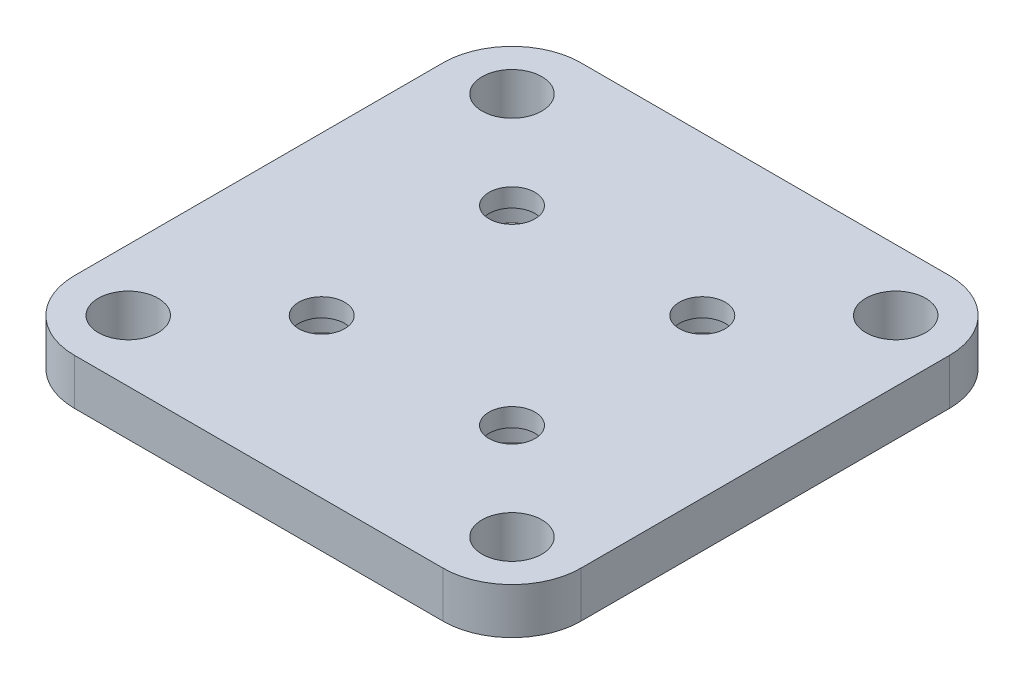
SolidWorks part; units mm, degrees
ref_plane "Front Plane" through (0, 0, 0) normal (0, 0, 1) x (1, 0, 0)
ref_plane "Top Plane" through (0, 0, 0) normal (0, 1, 0) x (1, 0, 0)
ref_plane "Right Plane" through (0, 0, 0) normal (1, 0, 0) x (0, 0, -1)
sketch "Sketch1" plane through (0, 0, 0) normal (0, 1, 0) x (1, 0, 0)
  line L1 (-27.55, -27.55) -> (27.55, -27.55)
  line L2 (-27.55, -27.55) -> (-27.55, 27.55)
  line L3 (-27.55, 27.55) -> (27.55, 27.55)
  line L4 (27.55, -27.55) -> (27.55, 27.55)
  line L5 (-27.55, -27.55) -> (27.55, 27.55) construction
  line L6 (-27.55, 27.55) -> (27.55, -27.55) construction
  point P0 (0, 0)
  dimension "D1" = 55.1
  dimension "D2" = 55.1
extrude "Boss-Extrude1" add sketch "Sketch1" along normal blind 5
fillet "Fillet1" radius 7.5 4 edges at (-27.55, 2.5, 27.55) (-27.55, 2.5, -27.55) (27.55, 2.5, -27.55) (27.55, 2.5, 27.55)
sketch "Sketch2" plane through (0, 5, 0) normal (0, 1, 0) x (1, 0, 0)
  line L0 (-27.5541, -28.5805) -> (28.5767, -28.5805)
  line L1 (-27.5541, -28.5805) -> (-27.5541, 27.5503)
  line L2 (-27.5541, 27.5503) -> (28.5767, 27.5503)
  line L3 (28.5767, -28.5805) -> (28.5767, 27.5503)
  line L4 (-27.5541, -28.5805) -> (28.5767, 27.5503) construction
  line L5 (-27.5541, 27.5503) -> (28.5767, -28.5805) construction
  circle A0 centre (20.8659, -20.8697) radius 3.25
  circle A1 centre (-20.8741, -20.8697) radius 3.25
  circle A2 centre (-20.8741, 20.8703) radius 3.25
  circle A3 centre (20.8659, 20.8703) radius 3.25
  point P0 (0.5113, -0.5151)
extrude "Cut-Extrude1" cut sketch "Sketch2" against normal through all contours A2 | A1 | A3 | A0
sketch "Sketch3" plane through (0, 5, 0) normal (0, 1, 0) x (1, 0, 0)
  line L1 (-20, -20) -> (20, -20)
  line L2 (-20, -20) -> (-20, 20)
  line L3 (-20, 20) -> (20, 20)
  line L4 (20, -20) -> (20, 20)
  line L5 (-20, -20) -> (20, 20) construction
  line L6 (-20, 20) -> (20, -20) construction
  circle A0 centre (10.35, 10.35) radius 2.5
  circle A1 centre (-10.35, 10.35) radius 2.5
  circle A2 centre (-10.35, -10.35) radius 2.5
  circle A3 centre (10.35, -10.35) radius 2.5
  point P0 (0, 0)
  dimension "D5" = 5
  dimension "D7" = 9.65
  dimension "D8" = 5
  dimension "D9" = 5
  dimension "D12" = 9.65
  dimension "D13" = 9.65
  dimension "D14" = 5
  dimension "D1" = 40
  dimension "D2" = 40
  dimension "D3" = 9.65
  dimension "D4" = 9.65
  dimension "D6" = 9.65
  dimension "D10" = 9.65
  dimension "D11" = 9.65
extrude "Cut-Extrude2" cut sketch "Sketch3" against normal blind 5 contours A1 | A0 | A2 | A3
sketch "Sketch4" plane through (0, 0, 0) normal (0, -1, 0) x (1, 0, 0)
  circle A0 centre (-10.35, 10.35) radius 4.75
  circle A1 centre (10.35, 10.35) radius 4.75
  circle A2 centre (10.35, -10.35) radius 4.75
  circle A3 centre (-10.35, -10.35) radius 4.75
  dimension "D1" = 9.5
  dimension "D2" = 9.5
  dimension "D3" = 9.5
  dimension "D4" = 9.5
extrude "Cut-Extrude3" cut sketch "Sketch4" against normal blind 3
